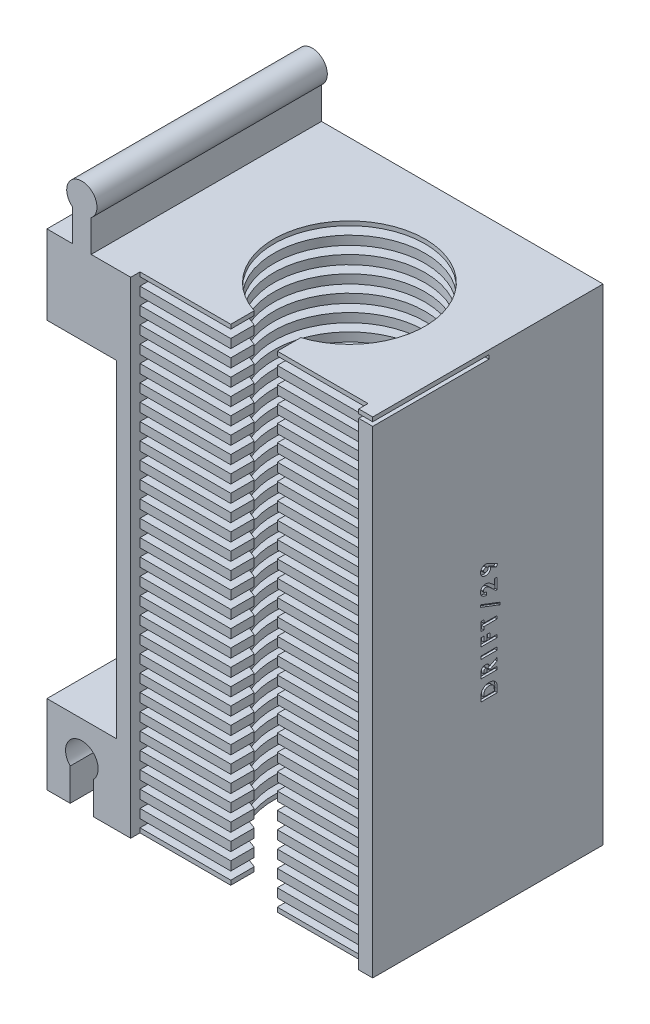
SolidWorks part; units mm, degrees
ref_plane "Plan de face" through (0, 0, 0) normal (0, 0, 1) x (1, 0, 0)
ref_plane "Plan de dessus" through (0, 0, 0) normal (0, 1, 0) x (1, 0, 0)
ref_plane "Plan de droite" through (0, 0, 0) normal (1, 0, 0) x (0, 0, -1)
sketch "Esquisse1" plane through (0, 0, 0) normal (0, 0, 1) x (1, 0, 0)
  line L1 (-20.1477, 24.3067) -> (34.8523, 24.3067)
  line L2 (-20.1477, 24.3067) -> (-20.1477, -82.2433)
  line L3 (-20.1477, -82.2433) -> (34.8523, -82.2433)
  line L4 (34.8523, 24.3067) -> (34.8523, -82.2433)
  dimension "D1" = 55
  dimension "D2" = 106.55
extrude "Boss.-Extru.2" add sketch "Esquisse1" along normal blind 49.5
sketch "Esquisse6" plane through (0, 0, 49.5) normal (0, 0, 1) x (1, 0, 0)
  line L0 (-20.1477, -82.2433) -> (34.8523, -82.2433) construction
  line L1 (-17.1477, 19.5067) -> (31.8523, 19.5067)
  line L2 (-17.1477, 19.5067) -> (-17.1477, -82.2433)
  line L3 (-17.1477, -82.2433) -> (31.8523, -82.2433)
  line L4 (31.8523, 19.5067) -> (31.8523, -82.2433)
  line L5 (-20.1477, 24.3067) -> (-20.1477, -82.2433) construction
  dimension "D1" = 49
  dimension "D2" = 3
  dimension "D3" = 101.75
extrude "Enlèv. mat.-Extru.2" cut sketch "Esquisse6" against normal blind 47
sketch "Esquisse7" plane through (0, 0, 2.5) normal (0, 0, 1) x (1, 0, 0)
  line L0 (31.8523, -82.2433) -> (31.8523, 19.5067) construction
  line L1 (-17.1477, -82.2433) -> (31.8523, -82.2433)
  line L2 (-17.1477, -82.2433) -> (-17.1477, -80.3433)
  line L3 (-17.1477, -80.3433) -> (31.8523, -80.3433)
  line L4 (31.8523, -82.2433) -> (31.8523, -80.3433)
  line L5 (-17.1477, -78.6433) -> (-17.1477, -76.7433)
  line L6 (-17.1477, -78.6433) -> (31.8523, -78.6433)
  line L7 (31.8523, -78.6433) -> (31.8523, -76.7433)
  line L8 (-17.1477, -76.7433) -> (31.8523, -76.7433)
  line L9 (-17.1477, -75.0433) -> (-17.1477, -73.1433)
  line L10 (-17.1477, -75.0433) -> (31.8523, -75.0433)
  line L11 (31.8523, -75.0433) -> (31.8523, -73.1433)
  line L12 (-17.1477, -73.1433) -> (31.8523, -73.1433)
  line L13 (-17.1477, -71.4433) -> (-17.1477, -69.5433)
  line L14 (-17.1477, -71.4433) -> (31.8523, -71.4433)
  line L15 (31.8523, -71.4433) -> (31.8523, -69.5433)
  line L16 (-17.1477, -69.5433) -> (31.8523, -69.5433)
  line L17 (-17.1477, -67.8433) -> (-17.1477, -65.9433)
  line L18 (-17.1477, -67.8433) -> (31.8523, -67.8433)
  line L19 (31.8523, -67.8433) -> (31.8523, -65.9433)
  line L20 (-17.1477, -65.9433) -> (31.8523, -65.9433)
  line L21 (-17.1477, -64.2433) -> (-17.1477, -62.3433)
  line L22 (-17.1477, -64.2433) -> (31.8523, -64.2433)
  line L23 (31.8523, -64.2433) -> (31.8523, -62.3433)
  line L24 (-17.1477, -62.3433) -> (31.8523, -62.3433)
  line L25 (-17.1477, -60.6433) -> (-17.1477, -58.7433)
  line L26 (-17.1477, -60.6433) -> (31.8523, -60.6433)
  line L27 (31.8523, -60.6433) -> (31.8523, -58.7433)
  line L28 (-17.1477, -58.7433) -> (31.8523, -58.7433)
  line L29 (-17.1477, -57.0433) -> (-17.1477, -55.1433)
  line L30 (-17.1477, -57.0433) -> (31.8523, -57.0433)
  line L31 (31.8523, -57.0433) -> (31.8523, -55.1433)
  line L32 (-17.1477, -55.1433) -> (31.8523, -55.1433)
  line L33 (-17.1477, -53.4433) -> (-17.1477, -51.5433)
  line L34 (-17.1477, -53.4433) -> (31.8523, -53.4433)
  line L35 (31.8523, -53.4433) -> (31.8523, -51.5433)
  line L36 (-17.1477, -51.5433) -> (31.8523, -51.5433)
  line L37 (-17.1477, -49.8433) -> (-17.1477, -47.9433)
  line L38 (-17.1477, -49.8433) -> (31.8523, -49.8433)
  line L39 (31.8523, -49.8433) -> (31.8523, -47.9433)
  line L40 (-17.1477, -47.9433) -> (31.8523, -47.9433)
  line L41 (-17.1477, -46.2433) -> (-17.1477, -44.3433)
  line L42 (-17.1477, -46.2433) -> (31.8523, -46.2433)
  line L43 (31.8523, -46.2433) -> (31.8523, -44.3433)
  line L44 (-17.1477, -44.3433) -> (31.8523, -44.3433)
  line L45 (-17.1477, -42.6433) -> (-17.1477, -40.7433)
  line L46 (-17.1477, -42.6433) -> (31.8523, -42.6433)
  line L47 (31.8523, -42.6433) -> (31.8523, -40.7433)
  line L48 (-17.1477, -40.7433) -> (31.8523, -40.7433)
  line L49 (-17.1477, -39.0433) -> (-17.1477, -37.1433)
  line L50 (-17.1477, -39.0433) -> (31.8523, -39.0433)
  line L51 (31.8523, -39.0433) -> (31.8523, -37.1433)
  line L52 (-17.1477, -37.1433) -> (31.8523, -37.1433)
  line L53 (-17.1477, -35.4433) -> (-17.1477, -33.5433)
  line L54 (-17.1477, -35.4433) -> (31.8523, -35.4433)
  line L55 (31.8523, -35.4433) -> (31.8523, -33.5433)
  line L56 (-17.1477, -33.5433) -> (31.8523, -33.5433)
  line L57 (-17.1477, -31.8433) -> (-17.1477, -29.9433)
  line L58 (-17.1477, -31.8433) -> (31.8523, -31.8433)
  line L59 (31.8523, -31.8433) -> (31.8523, -29.9433)
  line L60 (-17.1477, -29.9433) -> (31.8523, -29.9433)
  line L61 (-17.1477, -28.2433) -> (-17.1477, -26.3433)
  line L62 (-17.1477, -28.2433) -> (31.8523, -28.2433)
  line L63 (31.8523, -28.2433) -> (31.8523, -26.3433)
  line L64 (-17.1477, -26.3433) -> (31.8523, -26.3433)
  line L65 (-17.1477, -24.6433) -> (-17.1477, -22.7433)
  line L66 (-17.1477, -24.6433) -> (31.8523, -24.6433)
  line L67 (31.8523, -24.6433) -> (31.8523, -22.7433)
  line L68 (-17.1477, -22.7433) -> (31.8523, -22.7433)
  line L69 (-17.1477, -21.0433) -> (-17.1477, -19.1433)
  line L70 (-17.1477, -21.0433) -> (31.8523, -21.0433)
  line L71 (31.8523, -21.0433) -> (31.8523, -19.1433)
  line L72 (-17.1477, -19.1433) -> (31.8523, -19.1433)
  line L73 (-17.1477, -17.4433) -> (-17.1477, -15.5433)
  line L74 (-17.1477, -17.4433) -> (31.8523, -17.4433)
  line L75 (31.8523, -17.4433) -> (31.8523, -15.5433)
  line L76 (-17.1477, -15.5433) -> (31.8523, -15.5433)
  line L77 (-17.1477, -13.8433) -> (-17.1477, -11.9433)
  line L78 (-17.1477, -13.8433) -> (31.8523, -13.8433)
  line L79 (31.8523, -13.8433) -> (31.8523, -11.9433)
  line L80 (-17.1477, -11.9433) -> (31.8523, -11.9433)
  line L81 (-17.1477, -10.2433) -> (-17.1477, -8.3433)
  line L82 (-17.1477, -10.2433) -> (31.8523, -10.2433)
  line L83 (31.8523, -10.2433) -> (31.8523, -8.3433)
  line L84 (-17.1477, -8.3433) -> (31.8523, -8.3433)
  line L85 (-17.1477, -6.6433) -> (-17.1477, -4.7433)
  line L86 (-17.1477, -6.6433) -> (31.8523, -6.6433)
  line L87 (31.8523, -6.6433) -> (31.8523, -4.7433)
  line L88 (-17.1477, -4.7433) -> (31.8523, -4.7433)
  line L89 (-17.1477, -3.0433) -> (-17.1477, -1.1433)
  line L90 (-17.1477, -3.0433) -> (31.8523, -3.0433)
  line L91 (31.8523, -3.0433) -> (31.8523, -1.1433)
  line L92 (-17.1477, -1.1433) -> (31.8523, -1.1433)
  line L93 (-17.1477, 0.5567) -> (-17.1477, 2.4567)
  line L94 (-17.1477, 0.5567) -> (31.8523, 0.5567)
  line L95 (31.8523, 0.5567) -> (31.8523, 2.4567)
  line L96 (-17.1477, 2.4567) -> (31.8523, 2.4567)
  line L97 (-17.1477, 4.1567) -> (-17.1477, 6.0567)
  line L98 (-17.1477, 4.1567) -> (31.8523, 4.1567)
  line L99 (31.8523, 4.1567) -> (31.8523, 6.0567)
  line L100 (-17.1477, 6.0567) -> (31.8523, 6.0567)
  line L101 (-17.1477, 7.7567) -> (-17.1477, 9.6567)
  line L102 (-17.1477, 7.7567) -> (31.8523, 7.7567)
  line L103 (31.8523, 7.7567) -> (31.8523, 9.6567)
  line L104 (-17.1477, 9.6567) -> (31.8523, 9.6567)
  line L105 (-17.1477, 11.3567) -> (-17.1477, 13.2567)
  line L106 (-17.1477, 11.3567) -> (31.8523, 11.3567)
  line L107 (31.8523, 11.3567) -> (31.8523, 13.2567)
  line L108 (-17.1477, 13.2567) -> (31.8523, 13.2567)
  line L109 (-17.1477, 14.9567) -> (-17.1477, 16.8567)
  line L110 (-17.1477, 14.9567) -> (31.8523, 14.9567)
  line L111 (31.8523, 14.9567) -> (31.8523, 16.8567)
  line L112 (-17.1477, 16.8567) -> (31.8523, 16.8567)
  line L113 (-17.1477, 18.5567) -> (-17.1477, 20.4567)
  line L114 (-17.1477, 18.5567) -> (31.8523, 18.5567)
  line L115 (31.8523, 18.5567) -> (31.8523, 20.4567)
  line L116 (-17.1477, 20.4567) -> (31.8523, 20.4567)
  dimension "D1" = 1.9
  dimension "D2" = 29
extrude "Boss.-Extru.3" add sketch "Esquisse7" along normal blind 45
sketch "Esquisse8" plane through (0, -82.2433, 0) normal (0, -1, 0) x (1, 0, 0)
  line L0 (-17.1477, 47.5) -> (-17.1477, 49.5) construction
  line L1 (-20.1477, 49.5) -> (-20.1477, 0) construction
  circle A0 centre (7.3523, 27) radius 16.25
  point P4 (-17.1477, 48.5)
  dimension "D1" = 32.5
  dimension "D2" = 21.5
  dimension "D3" = 27.5
extrude "Enlèv. mat.-Extru.4" cut sketch "Esquisse8" against normal through all
sketch "Esquisse9" plane through (0, -82.2433, 0) normal (0, -1, 0) x (1, 0, 0)
  line L0 (2.3523, 47.5) -> (2.3523, 42.4616)
  line L1 (-17.1477, 47.5) -> (31.8523, 47.5) construction
  line L2 (12.3523, 47.5) -> (12.3523, 42.4616)
  line L3 (2.3523, 47.5) -> (12.3523, 47.5)
  line L4 (-20.1477, 49.5) -> (-20.1477, 0) construction
  line L5 (2.3523, 42.4616) -> (12.3523, 42.4616)
  circle A0 centre (7.3523, 27) radius 16.25 construction
  dimension "D1" = 10
  dimension "D2" = 22.5
extrude "Enlèv. mat.-Extru.5" cut sketch "Esquisse9" against normal through all
sketch "Esquisse10" plane through (0, -82.2433, 0) normal (0, -1, 0) x (1, 0, 0)
  line L11 (31.8523, 47.5) -> (12.3523, 47.5)
  line L12 (12.3523, 47.5) -> (12.3523, 42.4616)
  line L13 (2.3523, 42.4616) -> (2.3523, 47.5)
  line L14 (2.3523, 47.5) -> (-17.1477, 47.5)
  line L15 (-17.1477, 47.5) -> (-17.1477, 49.5)
  line L16 (-17.1477, 49.5) -> (-20.1477, 49.5)
  line L17 (-20.1477, 49.5) -> (-20.1477, 0)
  line L18 (-20.1477, 0) -> (34.8523, 0)
  line L19 (34.8523, 0) -> (34.8523, 49.5)
  line L20 (34.8523, 49.5) -> (31.8523, 49.5)
  line L21 (31.8523, 49.5) -> (31.8523, 47.5)
  line L22 (31.8523, 47.5) -> (12.3523, 47.5)
  line L23 (12.3523, 47.5) -> (12.3523, 42.4616)
  line L24 (2.3523, 42.4616) -> (2.3523, 47.5)
  line L25 (2.3523, 47.5) -> (-17.1477, 47.5)
  line L26 (-17.1477, 47.5) -> (-17.1477, 49.5)
  line L27 (-17.1477, 49.5) -> (-20.1477, 49.5)
  line L28 (-20.1477, 49.5) -> (-20.1477, 0)
  line L29 (-20.1477, 0) -> (34.8523, 0)
  line L30 (34.8523, 0) -> (34.8523, 49.5)
  line L31 (34.8523, 49.5) -> (31.8523, 49.5)
  line L32 (31.8523, 49.5) -> (31.8523, 47.5)
  arc A1 (2.3523, 42.4616) -> (12.3523, 42.4616) centre (7.3523, 27) ccw
  arc A2 (2.3523, 42.4616) -> (12.3523, 42.4616) centre (7.3523, 27) ccw
  dimension "D1" = 0
sketch "Esquisse11" plane through (0, 24.3067, 0) normal (0, 1, 0) x (1, 0, 0)
  line L4 (34.8523, 0) -> (-20.1477, 0)
  line L5 (-20.1477, 0) -> (-20.1477, -49.5)
  line L6 (-20.1477, -49.5) -> (34.8523, -49.5)
  line L7 (34.8523, -49.5) -> (34.8523, 0)
  line L8 (34.8523, 0) -> (-20.1477, 0)
  line L9 (-20.1477, 0) -> (-20.1477, -49.5)
  line L10 (-20.1477, -49.5) -> (34.8523, -49.5)
  line L11 (34.8523, -49.5) -> (34.8523, 0)
  dimension "D1" = 0
extrude "Enlèv. mat.-Extru.6" cut sketch "Esquisse11" against normal blind 4.8
sketch "Esquisse14" plane through (0, 0, 49.5) normal (0, 0, 1) x (1, 0, 0)
  line L1 (34.8523, -82.2433) -> (49.8523, -82.2433)
  line L2 (34.8523, -82.2433) -> (34.8523, -64.2933)
  line L3 (34.8523, -64.2933) -> (49.8523, -64.2933)
  line L4 (49.8523, -82.2433) -> (49.8523, -64.2933)
  dimension "D1" = 15
  dimension "D2" = 17.95
extrude "Boss.-Extru.5" add sketch "Esquisse14" against normal up to surface (49.5 mm away) up to face at (7.3523, -31.3683, 0)
sketch "Esquisse15" plane through (0, 0, 49.5) normal (0, 0, 1) x (1, 0, 0)
  line L1 (-20.1477, -82.2433) -> (-35.1477, -82.2433)
  line L2 (-20.1477, -82.2433) -> (-20.1477, -64.2933)
  line L3 (-20.1477, -64.2933) -> (-35.1477, -64.2933)
  line L4 (-35.1477, -82.2433) -> (-35.1477, -64.2933)
  dimension "D1" = 17.95
  dimension "D2" = 15
extrude "Boss.-Extru.6" add sketch "Esquisse15" against normal up to surface (49.5 mm away) up to face at (21.5189, -42.3433, 0)
sketch "Esquisse16" plane through (0, 0, 49.5) normal (0, 0, 1) x (1, 0, 0)
  line L1 (34.8523, 19.5067) -> (49.8523, 19.5067)
  line L2 (34.8523, 19.5067) -> (34.8523, 2.5067)
  line L3 (34.8523, 2.5067) -> (49.8523, 2.5067)
  line L4 (49.8523, 19.5067) -> (49.8523, 2.5067)
  dimension "D1" = 17
  dimension "D2" = 15
extrude "Boss.-Extru.7" add sketch "Esquisse16" against normal up to surface (49.5 mm away) up to face at (7.3523, -47.8308, 0)
sketch "Esquisse17" plane through (0, 0, 49.5) normal (0, 0, 1) x (1, 0, 0)
  line L1 (-20.1477, 19.5067) -> (-35.1477, 19.5067)
  line L2 (-20.1477, 19.5067) -> (-20.1477, 2.5067)
  line L3 (-20.1477, 2.5067) -> (-35.1477, 2.5067)
  line L4 (-35.1477, 19.5067) -> (-35.1477, 2.5067)
  dimension "D1" = 15
  dimension "D2" = 17
extrude "Boss.-Extru.8" add sketch "Esquisse17" against normal up to surface (49.5 mm away) up to face at (15.8523, -37.7633, 0)
sketch "Esquisse18" plane through (0, 0, 49.5) normal (0, 0, 1) x (1, 0, 0)
  line L0 (44.8523, -74.3433) -> (44.8523, -82.2433)
  line L2 (44.8523, -82.2433) -> (39.8523, -82.2433)
  line L3 (39.8523, -82.2433) -> (39.8523, -74.3433)
  line L4 (7.3523, -82.2443) -> (7.3523, -64.1566) construction
  line L5 (49.8523, -82.2433) -> (49.8523, -64.2933) construction
  line L7 (-30.1477, -82.2433) -> (-25.1477, -82.2433)
  line L8 (-30.1477, -74.3433) -> (-30.1477, -82.2433)
  line L9 (-25.1477, -82.2433) -> (-25.1477, -74.3433)
  line L15 (31.8523, -82.2433) -> (49.8523, -82.2433) construction
  arc A0 (44.8523, -74.3433) -> (39.8523, -74.3433) centre (42.3523, -71.8938) ccw
  arc A1 (-30.1477, -74.3433) -> (-25.1477, -74.3433) centre (-27.6477, -71.8938) cw
  dimension "D5" = 3.5
  dimension "D1" = 5
  dimension "D2" = 5
  dimension "D3" = 7.9
  dimension "D4" = 7.9
extrude "Enlèv. mat.-Extru.8" cut sketch "Esquisse18" against normal through all
sketch "Esquisse20" plane through (0, 0, 49.5) normal (0, 0, 1) x (1, 0, 0)
  line L0 (-29.6477, 29.9467) -> (-29.6477, 19.5067)
  line L1 (-35.1477, 19.5067) -> (-17.1477, 19.5067) construction
  line L2 (-29.6477, 19.5067) -> (-25.6477, 19.5067)
  line L3 (-25.6477, 19.5067) -> (-25.6477, 29.9467)
  line L4 (-35.1477, 19.5067) -> (-35.1477, 2.5067) construction
  line L5 (7.3523, 19.5067) -> (7.3523, 35.4205) construction
  line L6 (23.6023, 19.5067) -> (-8.8977, 19.5067) construction
  line L7 (40.3523, 19.5067) -> (40.3523, 29.9467)
  line L8 (44.3523, 19.5067) -> (40.3523, 19.5067)
  line L9 (44.3523, 29.9467) -> (44.3523, 19.5067)
  arc A0 (-25.6477, 29.9467) -> (-29.6477, 29.9467) centre (-27.6477, 32.5084) ccw
  arc A1 (40.3523, 29.9467) -> (44.3523, 29.9467) centre (42.3523, 32.5084) cw
  dimension "D3" = 3.25
  dimension "D1" = 5.5
  dimension "D2" = 4
  dimension "D4" = 10.44
  dimension "D5" = 10.44
extrude "Boss.-Extru.9" add sketch "Esquisse20" against normal up to surface (49.5 mm away) up to face at (7.3523, -49.3534, 0)
extrude "Enlèv. mat.-Extru.10" cut sketch "Esquisse10" against normal blind 0.95
sketch "Esquisse22" plane through (0, -82.2433, 0) normal (0, -1, 0) x (1, 0, 0)
  line L0 (49.8523, 49.5) -> (44.8523, 49.5) construction
  line L1 (44.8523, 49.5) -> (44.8523, 0) construction
  line L2 (44.8523, 0) -> (49.8523, 0) construction
  line L3 (49.8523, 0) -> (49.8523, 49.5) construction
  line L4 (39.8523, 49.5) -> (34.8523, 49.5) construction
  line L5 (34.8523, 49.5) -> (34.8523, 0) construction
  line L6 (34.8523, 0) -> (39.8523, 0) construction
  line L7 (39.8523, 0) -> (39.8523, 49.5) construction
  line L8 (-35.1477, 0) -> (-30.1477, 0) construction
  line L9 (-30.1477, 0) -> (-30.1477, 49.5) construction
  line L10 (-30.1477, 49.5) -> (-35.1477, 49.5) construction
  line L11 (-35.1477, 49.5) -> (-35.1477, 0) construction
  line L12 (-25.1477, 0) -> (-20.1477, 0) construction
  line L13 (-20.1477, 0) -> (-20.1477, 49.5) construction
  line L14 (-20.1477, 49.5) -> (-25.1477, 49.5) construction
  line L15 (-25.1477, 49.5) -> (-25.1477, 0) construction
  line L16 (49.8523, 49.5) -> (44.8523, 49.5)
  line L17 (44.8523, 49.5) -> (44.8523, 0)
  line L18 (44.8523, 0) -> (49.8523, 0)
  line L19 (49.8523, 0) -> (49.8523, 49.5)
  line L20 (39.8523, 49.5) -> (34.8523, 49.5)
  line L21 (34.8523, 49.5) -> (34.8523, 0)
  line L22 (34.8523, 0) -> (39.8523, 0)
  line L23 (39.8523, 0) -> (39.8523, 49.5)
  line L24 (-35.1477, 0) -> (-30.1477, 0)
  line L25 (-30.1477, 0) -> (-30.1477, 49.5)
  line L26 (-30.1477, 49.5) -> (-35.1477, 49.5)
  line L27 (-35.1477, 49.5) -> (-35.1477, 0)
  line L28 (-25.1477, 0) -> (-20.1477, 0)
  line L29 (-20.1477, 0) -> (-20.1477, 49.5)
  line L30 (-20.1477, 49.5) -> (-25.1477, 49.5)
  line L31 (-25.1477, 49.5) -> (-25.1477, 0)
extrude "Enlèv. mat.-Extru.11" cut sketch "Esquisse22" against normal up to surface (0.95 mm away) up to face at (7.3523, -81.2933, 36.7676)
sketch "Esquisse23" plane through (0, 19.5067, 0) normal (0, 1, 0) x (1, 0, 0)
  line L11 (40.3523, -49.5) -> (40.3523, 0)
  line L12 (40.3523, 0) -> (-25.6477, 0)
  line L13 (-25.6477, 0) -> (-25.6477, -49.5)
  line L14 (-25.6477, -49.5) -> (-17.1477, -49.5)
  line L15 (-17.1477, -49.5) -> (-17.1477, -47.5)
  line L16 (-17.1477, -47.5) -> (2.3523, -47.5)
  line L17 (2.3523, -47.5) -> (2.3523, -42.4616)
  line L18 (12.3523, -42.4616) -> (12.3523, -47.5)
  line L19 (12.3523, -47.5) -> (31.8523, -47.5)
  line L20 (31.8523, -47.5) -> (31.8523, -49.5)
  line L21 (31.8523, -49.5) -> (40.3523, -49.5)
  line L22 (40.3523, -49.5) -> (40.3523, 0)
  line L23 (40.3523, 0) -> (-25.6477, 0)
  line L24 (-25.6477, 0) -> (-25.6477, -49.5)
  line L25 (-25.6477, -49.5) -> (-17.1477, -49.5)
  line L26 (-17.1477, -49.5) -> (-17.1477, -47.5)
  line L27 (-17.1477, -47.5) -> (2.3523, -47.5)
  line L28 (2.3523, -47.5) -> (2.3523, -42.4616)
  line L29 (12.3523, -42.4616) -> (12.3523, -47.5)
  line L30 (12.3523, -47.5) -> (31.8523, -47.5)
  line L31 (31.8523, -47.5) -> (31.8523, -49.5)
  line L32 (31.8523, -49.5) -> (40.3523, -49.5)
  arc A1 (12.3523, -42.4616) -> (2.3523, -42.4616) centre (7.3523, -27) ccw
  arc A2 (12.3523, -42.4616) -> (2.3523, -42.4616) centre (7.3523, -27) ccw
  dimension "D1" = 0
extrude "Boss.-Extru.10" add sketch "Esquisse23" along normal blind 3.6
sketch "Esquisse24" plane through (0, 0, 47.5) normal (0, 0, 1) x (1, 0, 0)
  line L0 (-17.1477, 23.1067) -> (-17.1477, 18.5567) construction
  line L1 (31.8523, 20.4567) -> (-17.1477, 20.4567)
  line L2 (31.8523, 20.4567) -> (31.8523, 22.1567)
  line L3 (31.8523, 22.1567) -> (-17.1477, 22.1567)
  line L4 (-17.1477, 20.4567) -> (-17.1477, 22.1567)
  line L5 (31.8523, 20.4567) -> (-17.1477, 22.1567) construction
  line L6 (31.8523, 22.1567) -> (-17.1477, 20.4567) construction
  line L7 (31.8523, 18.5567) -> (31.8523, 23.1067) construction
  line L8 (-17.1477, 23.1067) -> (2.3523, 23.1067) construction
  point P0 (7.3523, 21.3067)
  dimension "D1" = 1.7
  dimension "D2" = 0.95
extrude "Enlèv. mat.-Extru.12" cut sketch "Esquisse24" against normal up to surface (45 mm away) up to face at (7.3523, 17.7067, 2.5)
sketch "Esquisse25" plane through (0, 2.5067, 0) normal (0, -1, 0) x (1, 0, 0)
  line L4 (-35.1477, 0) -> (-20.1477, 0)
  line L5 (-20.1477, 0) -> (-20.1477, 49.5)
  line L6 (-20.1477, 49.5) -> (-35.1477, 49.5)
  line L7 (-35.1477, 49.5) -> (-35.1477, 0)
  line L8 (-35.1477, 0) -> (-20.1477, 0)
  line L9 (-20.1477, 0) -> (-20.1477, 49.5)
  line L10 (-20.1477, 49.5) -> (-35.1477, 49.5)
  line L11 (-35.1477, 49.5) -> (-35.1477, 0)
  line L12 (34.8523, 0) -> (49.8523, 0)
  line L13 (49.8523, 0) -> (49.8523, 49.5)
  line L14 (49.8523, 49.5) -> (34.8523, 49.5)
  line L15 (34.8523, 49.5) -> (34.8523, 0)
  line L16 (34.8523, 0) -> (49.8523, 0)
  line L17 (49.8523, 0) -> (49.8523, 49.5)
  line L18 (49.8523, 49.5) -> (34.8523, 49.5)
  line L19 (34.8523, 49.5) -> (34.8523, 0)
  dimension "D1" = 0
  dimension "D2" = 0
extrude "Enlèv. mat.-Extru.13" cut sketch "Esquisse25" against normal blind 3.6
sketch "Esquisse26" plane through (0, 19.5067, 0) normal (0, 1, 0) x (1, 0, 0)
  line L4 (-29.6477, -49.5) -> (-29.6477, 0)
  line L5 (-29.6477, 0) -> (-35.1477, 0)
  line L6 (-35.1477, 0) -> (-35.1477, -49.5)
  line L7 (-35.1477, -49.5) -> (-29.6477, -49.5)
  line L8 (-29.6477, -49.5) -> (-29.6477, 0)
  line L9 (-29.6477, 0) -> (-35.1477, 0)
  line L10 (-35.1477, 0) -> (-35.1477, -49.5)
  line L11 (-35.1477, -49.5) -> (-29.6477, -49.5)
  line L12 (44.3523, 0) -> (44.3523, -49.5)
  line L13 (44.3523, -49.5) -> (49.8523, -49.5)
  line L14 (49.8523, -49.5) -> (49.8523, 0)
  line L15 (49.8523, 0) -> (44.3523, 0)
  line L16 (44.3523, 0) -> (44.3523, -49.5)
  line L17 (44.3523, -49.5) -> (49.8523, -49.5)
  line L18 (49.8523, -49.5) -> (49.8523, 0)
  line L19 (49.8523, 0) -> (44.3523, 0)
  dimension "D1" = 0
  dimension "D2" = 0
extrude "Boss.-Extru.11" add sketch "Esquisse26" along normal blind 3.6
sketch "Esquisse27" plane through (34.8523, 0, 0) normal (1, 0, 0) x (0, 0, -1)
  line L0 (-22.75, -64.2933) -> (-22.75, 6.1067) construction
  line L4 (-49.5, -64.2933) -> (-49.5, 6.1067) construction
  text T0 "<b>DRIFT/29</b>" font "Century Gothic" height 3.5
  dimension "D1" = 26.75
extrude "Enlèv. mat.-Extru.15" cut sketch "Esquisse27" against normal blind 0.5
sketch "Esquisse28" plane through (0, -64.2933, 0) normal (0, 1, 0) x (1, 0, 0)
  line L4 (49.8523, 0) -> (34.8523, 0)
  line L5 (34.8523, 0) -> (34.8523, -49.5)
  line L6 (34.8523, -49.5) -> (49.8523, -49.5)
  line L7 (49.8523, -49.5) -> (49.8523, 0)
  line L8 (49.8523, 0) -> (34.8523, 0)
  line L9 (34.8523, 0) -> (34.8523, -49.5)
  line L10 (34.8523, -49.5) -> (49.8523, -49.5)
  line L11 (49.8523, -49.5) -> (49.8523, 0)
  dimension "D1" = 0
extrude "Enlèv. mat.-Extru.16" cut sketch "Esquisse28" against normal through all
sketch "Esquisse29" plane through (0, 6.1067, 0) normal (0, -1, 0) x (1, 0, 0)
  line L4 (34.8523, 49.5) -> (34.8523, 0)
  line L5 (34.8523, 0) -> (49.8523, 0)
  line L6 (49.8523, 0) -> (49.8523, 49.5)
  line L7 (49.8523, 49.5) -> (34.8523, 49.5)
  line L8 (34.8523, 49.5) -> (34.8523, 0)
  line L9 (34.8523, 0) -> (49.8523, 0)
  line L10 (49.8523, 0) -> (49.8523, 49.5)
  line L11 (49.8523, 49.5) -> (34.8523, 49.5)
  dimension "D1" = 0
extrude "Enlèv. mat.-Extru.17" cut sketch "Esquisse29" against normal through all
sketch "Esquisse30" plane through (0, 22.1567, 0) normal (0, -1, 0) x (1, 0, 0)
  line L7 (2.3523, 42.4616) -> (2.3523, 47.5)
  line L8 (2.3523, 47.5) -> (-17.1477, 47.5)
  line L9 (-17.1477, 47.5) -> (-17.1477, 2.5)
  line L10 (-17.1477, 2.5) -> (31.8523, 2.5)
  line L11 (31.8523, 2.5) -> (31.8523, 47.5)
  line L12 (31.8523, 47.5) -> (12.3523, 47.5)
  line L13 (12.3523, 47.5) -> (12.3523, 42.4616)
  line L14 (2.3523, 42.4616) -> (2.3523, 47.5)
  line L15 (2.3523, 47.5) -> (-17.1477, 47.5)
  line L16 (-17.1477, 47.5) -> (-17.1477, 2.5)
  line L17 (-17.1477, 2.5) -> (31.8523, 2.5)
  line L18 (31.8523, 2.5) -> (31.8523, 47.5)
  line L19 (31.8523, 47.5) -> (12.3523, 47.5)
  line L20 (12.3523, 47.5) -> (12.3523, 42.4616)
  arc A1 (2.3523, 42.4616) -> (12.3523, 42.4616) centre (7.3523, 27) ccw
  arc A2 (2.3523, 42.4616) -> (12.3523, 42.4616) centre (7.3523, 27) ccw
  dimension "D1" = 0
extrude "Enlèv. mat.-Extru.18" cut sketch "Esquisse30" against normal blind 0.05
sketch "Esquisse31" plane through (31.8523, 0, 0) normal (-1, 0, 0) x (0, 0, 1)
  line L0 (49.5, -81.2933) -> (49.5, 23.1067) construction
  line L1 (24.5, 22.2067) -> (49.5, 22.2067)
  line L2 (24.5, 22.2067) -> (24.5, 21.3567)
  line L3 (24.5, 21.3567) -> (49.5, 21.3567)
  line L4 (49.5, 22.2067) -> (49.5, 21.3567)
  point P5 (0, 0)
  point P8 (0, 0)
  point P10 (0, 0)
  dimension "D1" = 0.85
  dimension "D2" = 25
extrude "Enlèv. mat.-Extru.19" cut sketch "Esquisse31" against normal through all
